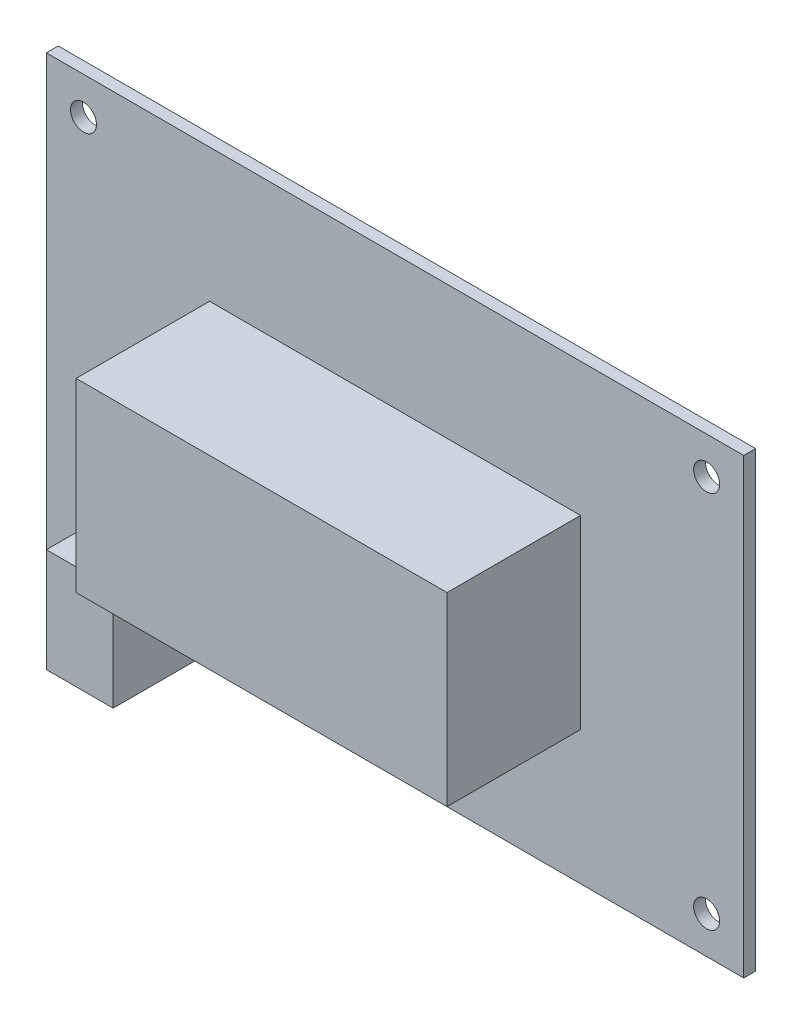
SolidWorks part; units mm, degrees
ref_plane "Plan de face" through (0, 0, 0) normal (0, 0, 1) x (1, 0, 0)
ref_plane "Plan de dessus" through (0, 0, 0) normal (0, 1, 0) x (1, 0, 0)
ref_plane "Plan de droite" through (0, 0, 0) normal (1, 0, 0) x (0, 0, -1)
sketch "Esquisse1" plane through (0, 0, 0) normal (0, 0, 1) x (1, 0, 0)
  line L1 (47, 30.5) -> (-47, 30.5)
  line L2 (47, 30.5) -> (47, -30.5)
  line L3 (47, -30.5) -> (-47, -30.5)
  line L4 (-47, 30.5) -> (-47, -30.5)
  line L5 (47, 30.5) -> (-47, -30.5) construction
  line L6 (47, -30.5) -> (-47, 30.5) construction
  circle A0 centre (-42, 25.5) radius 1.75
  circle A1 centre (42, 25.5) radius 1.75
  circle A2 centre (42, -25.5) radius 1.75
  circle A3 centre (-42, -25.5) radius 1.75
  point P1 (0, 0)
  point P16 (0, 0)
  dimension "D3" = 3.5
  dimension "D1" = 94
  dimension "D2" = 61
  dimension "D4" = 5
  dimension "D5" = 5
  dimension "D6" = 5
  dimension "D7" = 5
  dimension "D8" = 5
  dimension "D9" = 5
  dimension "D10" = 5
  dimension "D11" = 5
extrude "Boss.-Extru.1" add sketch "Esquisse1" along normal blind 1.6
sketch "Esquisse2" plane through (0, 0, 1.6) normal (0, 0, 1) x (1, 0, 0)
  line L1 (25, 12.5) -> (-25, 12.5)
  line L2 (25, 12.5) -> (25, -12.5)
  line L3 (25, -12.5) -> (-25, -12.5)
  line L4 (-25, 12.5) -> (-25, -12.5)
  line L5 (25, 12.5) -> (-25, -12.5) construction
  line L6 (25, -12.5) -> (-25, 12.5) construction
  point P0 (0, 0)
  dimension "D1" = 25
  dimension "D2" = 50
extrude "Boss.-Extru.2" add sketch "Esquisse2" along normal blind 18
sketch "Esquisse3" plane through (0, 0, 1.6) normal (0, 0, 1) x (1, 0, 0)
  line L0 (-47, -30.5) -> (47, -30.5) construction
  line L1 (-36, -30.5) -> (-27, -30.5)
  line L2 (-36, -30.5) -> (-36, -16.5)
  line L3 (-36, -16.5) -> (-27, -16.5)
  line L4 (-27, -30.5) -> (-27, -16.5)
  line L5 (-47, 30.5) -> (-47, -30.5) construction
  dimension "D1" = 9
  dimension "D2" = 14
  dimension "D3" = 11
extrude "Boss.-Extru.3" add sketch "Esquisse3" along normal blind 11
